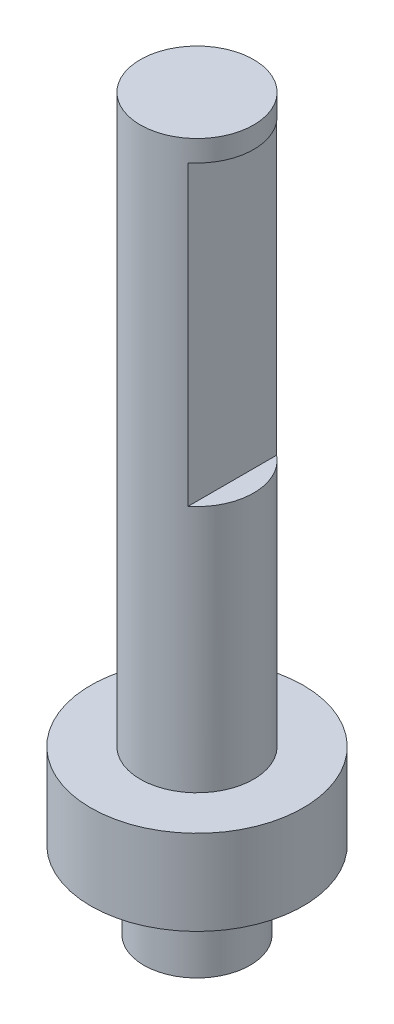
SolidWorks part; units mm, degrees
ref_plane "Front Plane" through (0, 0, 0) normal (0, 0, 1) x (1, 0, 0)
ref_plane "Top Plane" through (0, 0, 0) normal (0, 1, 0) x (1, 0, 0)
ref_plane "Right Plane" through (0, 0, 0) normal (1, 0, 0) x (0, 0, -1)
sketch "Sketch1" plane through (0, 0, 0) normal (0, 1, 0) x (1, 0, 0)
  circle A0 centre (0, 0) radius 7.5
  dimension "D1" = 15
extrude "Boss-Extrude1" add sketch "Sketch1" against normal blind 11
sketch "Sketch2" plane through (0, 0, 0) normal (0, 1, 0) x (1, 0, 0)
  circle A0 centre (0, 0) radius 15
  dimension "D1" = 30
extrude "Boss-Extrude2" add sketch "Sketch2" along normal blind 12
sketch "Sketch3" plane through (0, 12, 0) normal (0, 1, 0) x (1, 0, 0)
  circle A0 centre (0, 0) radius 8
  dimension "D1" = 16
extrude "Boss-Extrude3" add sketch "Sketch3" along normal blind 80
sketch "Sketch4" plane through (0, 0, 0) normal (0, 0, 1) x (1, 0, 0)
  line L0 (8, 92) -> (-8, 92) construction
  line L1 (14.8018, 89) -> (5, 89)
  line L2 (14.8018, 89) -> (14.8018, 47)
  line L3 (14.8018, 47) -> (5, 47)
  line L4 (5, 89) -> (5, 47)
  line L6 (-8, 92) -> (-8, 12) construction
  dimension "D1" = 3
  dimension "D2" = 13
  dimension "D3" = 42
extrude "Cut-Extrude1" cut sketch "Sketch4" against normal mid plane 80 contours L2 L3 L4 L1
